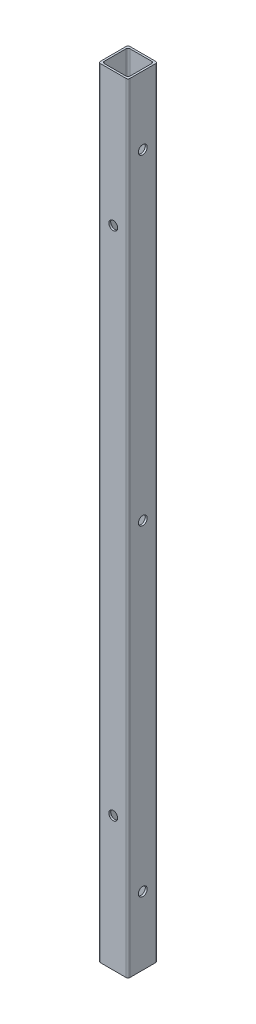
SolidWorks part; units mm, degrees
ref_plane "Front Plane" through (0, 0, 0) normal (0, 0, 1) x (1, 0, 0)
ref_plane "Top Plane" through (0, 0, 0) normal (0, 1, 0) x (1, 0, 0)
ref_plane "Right Plane" through (0, 0, 0) normal (1, 0, 0) x (0, 0, -1)
sketch "Sketch1" plane through (0, 0, 0) normal (0, 1, 0) x (1, 0, 0)
  line L0 (8.382, -8.382) -> (8.382, 8.382)
  line L1 (-9.652, -9.652) -> (9.652, -9.652)
  line L2 (-9.652, -9.652) -> (-9.652, 9.652)
  line L3 (-9.652, 9.652) -> (9.652, 9.652)
  line L4 (9.652, -9.652) -> (9.652, 9.652)
  line L5 (-9.652, -9.652) -> (9.652, 9.652) construction
  line L6 (-9.652, 9.652) -> (9.652, -9.652) construction
  line L7 (-8.382, 8.382) -> (8.382, 8.382)
  line L8 (-8.382, -8.382) -> (-8.382, 8.382)
  line L9 (-8.382, -8.382) -> (8.382, -8.382)
  point P0 (0, 0)
  dimension "D1" = 19.304
  dimension "D2" = 1.27
extrude "Boss-Extrude1" add sketch "Sketch1" along normal blind 508
fillet "Fillet1" radius 1.27 8 edges at (-9.652, 254, 9.652) (-9.652, 254, -9.652) (9.652, 254, -9.652) (9.652, 254, 9.652) (-8.382, 254, -8.382) (8.382, 254, 8.382) (8.382, 254, -8.382) (-8.382, 254, 8.382)
hole_wizard "#1 (0.228) Diameter Hole2" positions "Sketch4" profile "Sketch5" hole size "#1" standard "ANSI Inch" end condition through all
sketch "Sketch4" plane through (-9.652, 0, 0) normal (-1, 0, 0) x (0, 0, 1)
  line L0 (0, 0) -> (0, 508) construction
  line L1 (-8.382, 0) -> (8.382, 0) construction
  line L2 (-8.382, 508) -> (8.382, 508) construction
  point P8 (0, 44.45)
  point P34 (0, 254)
  point P35 (0, 463.55)
  dimension "D1" = 44.45
  dimension "D2" = 3
sketch "Sketch5" plane through (-9.652, 463.55, 0) normal (0, 1, 0) x (0, 0, 1)
  line L0 (0, 0) -> (0, 19.304)
  line L1 (0, 19.304) -> (2.8956, 19.304)
  line L2 (2.8956, 19.304) -> (2.8956, 0)
  line L5 (2.8956, 0) -> (0, 0)
  line L11 (0, -6.35) -> (0, 107.95) construction
  dimension "Thru Hole Dia." = 5.7912
  dimension "Thru Hole Depth" = 19.304
hole_wizard "#1 (0.228) Diameter Hole3" positions "Sketch6" profile "Sketch7" hole size "#1" standard "ANSI Inch" end condition through all
sketch "Sketch6" plane through (0, 0, -9.652) normal (0, 0, -1) x (-1, 0, 0)
  line L0 (0, 508) -> (0, 0) construction
  line L1 (-8.382, 508) -> (8.382, 508) construction
  point P8 (0, 87.3125)
  point P10 (0, 420.6875)
  dimension "D1" = 87.3125
  dimension "D2" = 333.375
sketch "Sketch7" plane through (0, 420.6875, -9.652) normal (1, 0, 0) x (0, 1, 0)
  line L0 (0, 0) -> (0, 19.304)
  line L1 (0, 19.304) -> (2.8956, 19.304)
  line L2 (2.8956, 19.304) -> (2.8956, 0)
  line L5 (2.8956, 0) -> (0, 0)
  line L11 (0, -6.35) -> (0, 107.95) construction
  dimension "Thru Hole Dia." = 5.7912
  dimension "Thru Hole Depth" = 19.304
